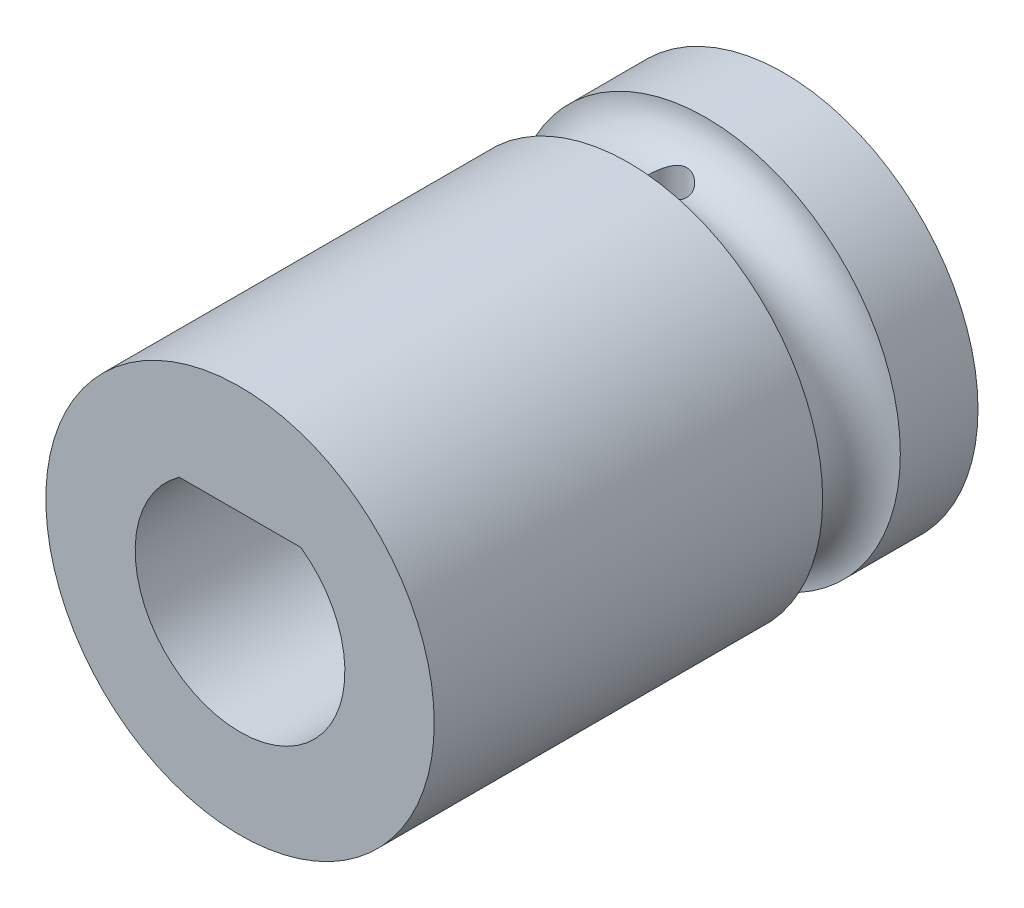
SolidWorks part; units mm, degrees
ref_plane "Front Plane" through (0, 0, 0) normal (0, 0, 1) x (1, 0, 0)
ref_plane "Top Plane" through (0, 0, 0) normal (0, 1, 0) x (1, 0, 0)
ref_plane "Right Plane" through (0, 0, 0) normal (1, 0, 0) x (0, 0, -1)
sketch "Sketch1" plane through (0, 0, 0) normal (0, 0, 1) x (1, 0, 0)
  line L0 (0, 0) -> (0, 2.2) construction
  line L1 (1.5652, 2.2) -> (-1.5652, 2.2)
  arc A0 (-1.5652, 2.2) -> (1.5652, 2.2) centre (0, 0) ccw
  circle A1 centre (0, 0) radius 5
  point P7 (0, 2.2)
  dimension "D1" = 5.4
  dimension "D3" = 10
  dimension "D2" = 2.2
extrude "Boss-Extrude1" add sketch "Sketch1" along normal blind 11 and the other way blind 3
sketch "Sketch2" plane through (0, 0, 0) normal (1, 0, 0) x (0, 0, -1)
  line L0 (0, 0) -> (0, 5) construction
  line L1 (3, 5) -> (-11, 5) construction
  line L2 (0, 0) -> (-4.1761, 0) construction
  line L3 (1, 5) -> (-1, 5)
  arc A0 (1, 5) -> (-1, 5) centre (0, 5) cw
  dimension "D1" = 1
revolve "Cut-Revolve1" cut sketch "Sketch2" angle 360 about L2
sketch "Sketch3" plane through (0, 0, 0) normal (0, 1, 0) x (1, 0, 0)
  circle A0 centre (0, 0) radius 0.5
  dimension "D1" = 1
extrude "Cut-Extrude1" cut sketch "Sketch3" along normal blind 11
sketch "Sketch4" plane through (0, 0, -3) normal (0, 0, -1) x (-1, 0, 0)
  line L0 (-1.5652, 2.2) -> (1.5652, 2.2) construction
  line L1 (-0.5, 2.2) -> (0.5, 2.2)
  arc A0 (0.5, 2.2) -> (-0.5, 2.2) centre (0, 2.2) ccw
  dimension "D1" = 0.5
extrude "Cut-Extrude2" cut sketch "Sketch4" against normal blind 3
